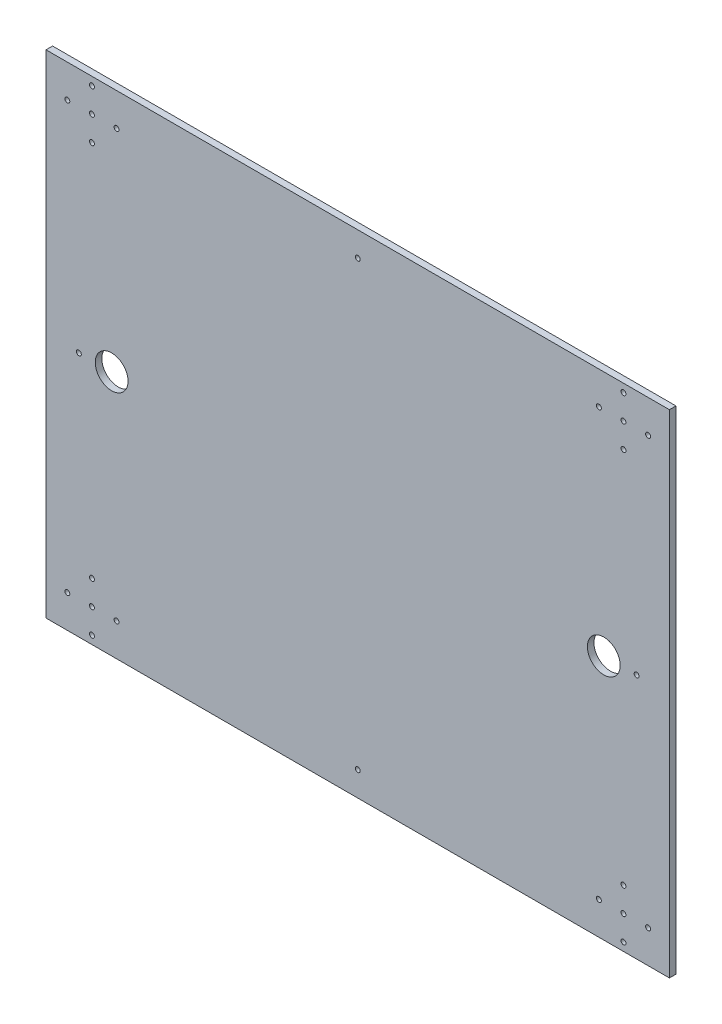
SolidWorks part; units mm, degrees
ref_plane "Front Plane" through (0, 0, 0) normal (0, 0, 1) x (1, 0, 0)
ref_plane "Top Plane" through (0, 0, 0) normal (0, 1, 0) x (1, 0, 0)
ref_plane "Right Plane" through (0, 0, 0) normal (1, 0, 0) x (0, 0, -1)
sketch "Sketch3" plane through (0, 0, 0) normal (0, 0, 1) x (1, 0, 0)
  line L0 (-313.1499, 197.7637) -> (66.8501, 197.7637)
  line L1 (66.8501, 197.7637) -> (66.8501, -102.2363)
  line L2 (66.8501, -102.2363) -> (-313.1499, -102.2363)
  line L3 (-313.1499, -102.2363) -> (-313.1499, 197.7637)
extrude "Boss-Extrude1" add sketch "Sketch3" along normal blind 4
hole_wizard "Hole2" positions "3DSketch4" profile "Sketch7" legacy
sketch3d "3DSketch4"
  line L0 (-313.1499, 197.7637, 4) -> (-313.1499, -102.2363, 4) construction
  line L1 (66.8501, 197.7637, 4) -> (-313.1499, 197.7637, 4) construction
  line L2 (66.8501, -102.2363, 4) -> (66.8501, 197.7637, 4) construction
  point P0 (-273.1499, 47.7637, 4)
  point P2 (26.8501, 47.7637, 4)
  dimension "D1" = 40
  dimension "D2" = 150
  dimension "D3" = 150
  dimension "D4" = 40
sketch "Sketch7" plane through (-273.1499, 47.7637, 4) normal (1, 0, 0) x (0, -1, 0)
  line L0 (0, 0) -> (0, 100)
  line L1 (0, 100) -> (10, 100)
  line L2 (10, 100) -> (10, 0)
  line L3 (10, 0) -> (0, 0)
  line L4 (0, 110) -> (0, -10) construction
  dimension "Diameter" = 20
  dimension "Depth" = 100
sketch "Sketch10" plane through (0, 0, 0) normal (0, 0, -1) x (-1, 0, 0)
  line L0 (313.1499, 197.7637) -> (313.1499, -102.2363) construction
  line L2 (-66.8501, 197.7637) -> (313.1499, 197.7637) construction
  circle A0 centre (285.1499, 177.7637) radius 1.5
  circle A1 centre (270.1499, 177.7637) radius 1.5
  circle A2 centre (285.1499, 192.7637) radius 1.5
  circle A3 centre (285.1499, 177.7637) radius 1.5
  circle A4 centre (300.1499, 177.7637) radius 1.5
  circle A5 centre (285.1499, 177.7637) radius 1.5
  circle A6 centre (285.1499, 162.7637) radius 1.5
  circle A7 centre (285.1499, 177.7637) radius 1.5
  circle A8 centre (-38.8501, 162.7637) radius 1.5
  circle A9 centre (-53.8501, 177.7637) radius 1.5
  circle A10 centre (-38.8501, 177.7637) radius 1.5
  circle A11 centre (-38.8501, 192.7637) radius 1.5
  circle A12 centre (-23.8501, 177.7637) radius 1.5
  circle A13 centre (-38.8501, -97.2363) radius 1.5
  circle A14 centre (-53.8501, -82.2363) radius 1.5
  circle A15 centre (-38.8501, -82.2363) radius 1.5
  circle A16 centre (-38.8501, -67.2363) radius 1.5
  circle A17 centre (-23.8501, -82.2363) radius 1.5
  circle A18 centre (285.1499, -97.2363) radius 1.5
  circle A19 centre (270.1499, -82.2363) radius 1.5
  circle A20 centre (285.1499, -82.2363) radius 1.5
  circle A21 centre (285.1499, -67.2363) radius 1.5
  circle A22 centre (300.1499, -82.2363) radius 1.5
  point P20 (285.1499, 177.7637)
  dimension "D1" = 28
  dimension "D2" = 20
  dimension "D3" = 15
  dimension "D7" = 13
  dimension "D5" = 2
  dimension "D6" = 2
  dimension "D4" = 4
extrude "Cut-Extrude1" cut sketch "Sketch10" against normal blind 4
sketch "Sketch11" plane through (0, 0, 0) normal (0, 0, -1) x (-1, 0, 0)
  circle A3 centre (293.1499, 47.7637) radius 1.5
  circle A7 centre (123.1499, 182.7637) radius 1.5
  circle A8 centre (-46.8501, 47.7637) radius 1.5
  circle A10 centre (123.1499, -87.2363) radius 1.5
extrude "Cut-Extrude2" cut sketch "Sketch11" against normal blind 4
